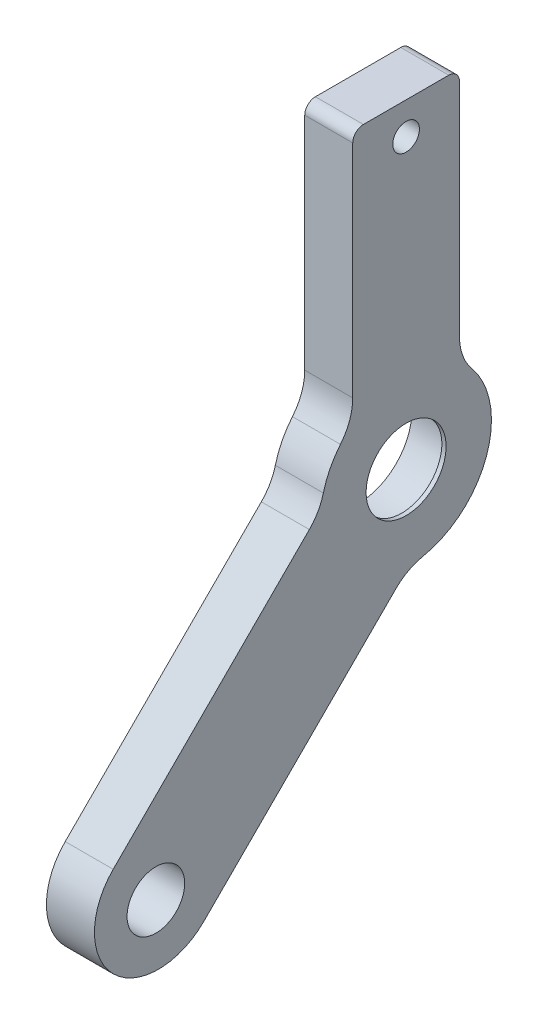
SolidWorks part; units mm, degrees
ref_plane "前视基准面" through (0, 0, 0) normal (0, 0, 1) x (1, 0, 0)
ref_plane "上视基准面" through (0, 0, 0) normal (0, 1, 0) x (1, 0, 0)
ref_plane "右视基准面" through (0, 0, 0) normal (1, 0, 0) x (0, 0, -1)
sketch "草图1" plane through (0, 0, 0) normal (-1, 0, 0) x (0, 0, 1)
  line L0 (-4, 30) -> (4, 30)
  line L2 (9.0672, -0.3462) -> (27.4519, -18.731)
  line L3 (5, 8.3066) -> (5, 29)
  line L5 (-5, 8.3066) -> (-5, 29)
  line L10 (0.9565, -9.2061) -> (18.9667, -27.2162)
  arc A0 (-6.1538, 5.1118) -> (-1.5871, -7.841) centre (0, 0) ccw
  arc A1 (7.7555, 1.9627) -> (6.1538, 5.1118) centre (0, 0) ccw
  arc A2 (27.4519, -18.731) -> (18.9667, -27.2162) centre (23.2093, -22.9736) cw
  arc A4 (0.9565, -9.2061) -> (-1.5871, -7.841) centre (-2.579, -12.7416) ccw
  arc A5 (-5, 8.3066) -> (-6.1538, 5.1118) centre (-10, 8.3066) cw
  arc A6 (9.0672, -0.3462) -> (7.7555, 1.9627) centre (12.6027, 3.1894) cw
  arc A7 (5, 8.3066) -> (6.1538, 5.1118) centre (10, 8.3066) ccw
  arc A8 (5, 29) -> (4, 30) centre (4, 29) ccw
  arc A9 (-5, 29) -> (-4, 30) centre (-4, 29) cw
  circle A11 centre (23.4521, -23.2164) radius 2.7
  point P3 (35.3553, -35.3553)
  point P5 (4, 1.6569)
  point P6 (38.1838, -32.5269)
  point P7 (5, 30)
  point P8 (-4, -1.6569)
  point P9 (32.5269, -38.1838)
  point P10 (-5, 30)
  point P19 (23.5839, -31.8335)
  point P22 (-0.2536, -7.996)
  point P25 (-5, 6.245)
  point P28 (7.9641, 0.7569)
  dimension "D1" = 16
  dimension "D3" = 33
  dimension "D6" = 5
  dimension "D7" = 5
  dimension "D8" = 1
  dimension "D9" = 10
  dimension "D10" = 6
  dimension "D12" = 5.4
  dimension "D5" = 6
  dimension "D2" = 30
  dimension "D4" = 12
extrude "凸台-拉伸1" add sketch "草图1" along normal mid plane 4.5
sketch "草图4" plane through (2.25, 0, 0) normal (-1, 0, 0) x (0, 0, 1)
  circle A0 centre (0, 0) radius 3.75
  dimension "D1" = 7.5
extrude "切除-拉伸2" cut sketch "草图4" along normal blind 5
sketch "草图7" plane through (-2.25, 0, 0) normal (-1, 0, 0) x (0, 0, 1)
  circle A0 centre (0, 0) radius 5.05
  dimension "D1" = 10.1
extrude "切除-拉伸4" cut sketch "草图7" against normal blind 4.1
sketch "草图8" plane through (2.25, 0, 0) normal (1, 0, 0) x (0, 0, -1)
  circle A0 centre (0, 27) radius 1.25
  dimension "D1" = 2.5
extrude "切除-拉伸5" cut sketch "草图8" against normal blind 6
